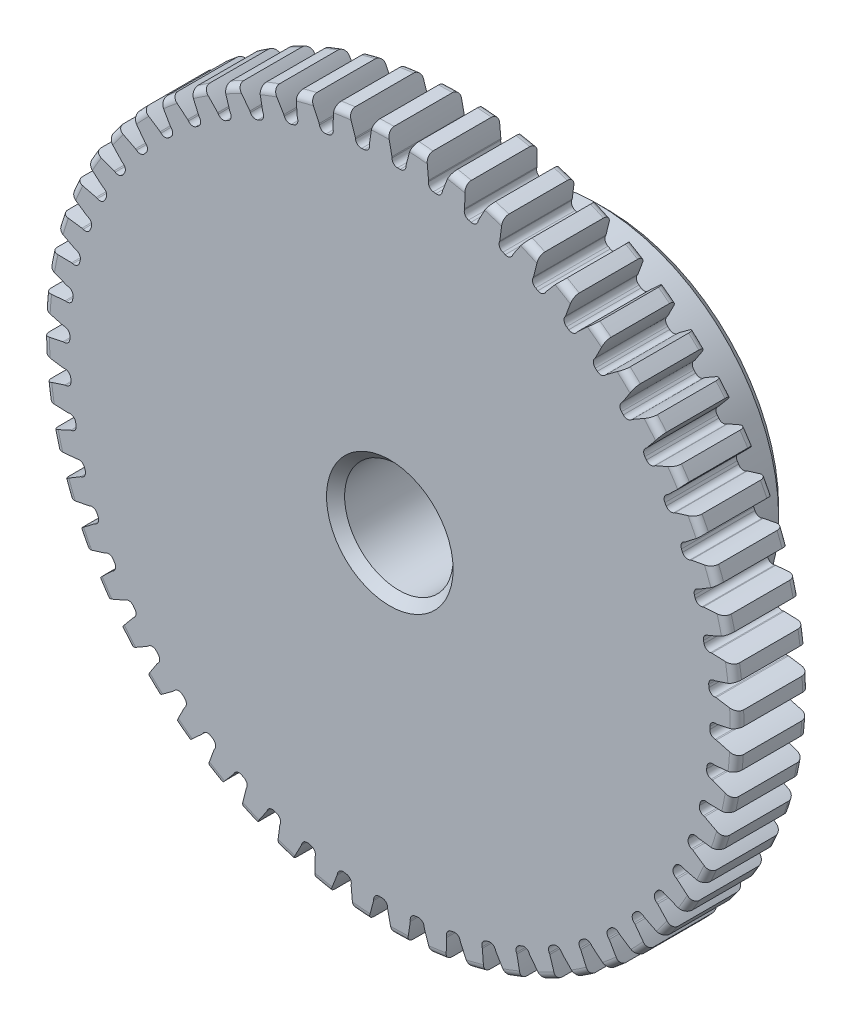
SolidWorks part; units mm, degrees
ref_plane "Front" through (0, 0, 0) normal (0, 0, 1) x (1, 0, 0)
ref_plane "Top" through (0, 0, 0) normal (0, 1, 0) x (1, 0, 0)
ref_plane "Right" through (0, 0, 0) normal (1, 0, 0) x (0, 0, -1)
sketch "Sketch1" plane through (0, 0, 0) normal (0, 0, 1) x (1, 0, 0)
  line L0 (-711.2, 0) -> (711.2, 0) construction
  circle A0 centre (0, 0) radius 15.24
  circle A1 centre (0, 0) radius 14.8209 construction
  circle A3 centre (0, 0) radius 14.049 construction
  dimension "D1" = 1.191
  dimension "OD" = 30.48
  dimension "Ptich Dia" = 29.6418
  dimension "Root Dia" = 28.0981
  dimension "D3" = 0.4191
  dimension "Number of Teeth" = 1422.4
extrude "Boss-Extrude1" add sketch "Sketch1" against normal blind 3.175
sketch "Sketch2" plane through (0, 0, 0) normal (1, 0, 0) x (0, 0, -1)
  line L0 (3.175, 0) -> (9.525, 0)
  line L1 (3.175, 0) -> (3.175, 7.9375)
  line L2 (3.175, 7.9375) -> (9.525, 7.9375)
  line L3 (9.525, 7.9375) -> (9.525, 0)
  point P5 (9.525, -7.9375)
  point P6 (0, -15.24)
  point P7 (3.175, -15.24)
  point P9 (0, 15.24)
  dimension "Face Wd" = 3.175
  dimension "B Hub Dia" = 15.875
  dimension "D O'all Lg." = 9.525
revolve "Revolve1" add sketch "Sketch2" angle 360 about L0
fillet "Fillet2" radius 0.3048 3 edges at (15.24, 0, -3.175) (15.24, 0, 0) (7.9375, 0, -3.175)
sketch "Sketch3" plane through (0, 0, 0) normal (0, 0, 1) x (1, 0, 0)
  line L0 (0, 0) -> (0, 15.24) construction
  line L1 (-3.5927, 13.8918) -> (0, 14.8209)
  line L2 (-9.5921, 14.8209) -> (9.5921, 14.8209) construction
  line L3 (-9.2865, 12.4192) -> (9.2865, 17.2226) construction
  line L4 (-3.5927, 13.8918) -> (0, 0) construction
  line L5 (-9.1637, 11.0416) -> (0, 0) construction
  line L6 (-9.1637, 11.0416) -> (-1.4732, 17.424) construction
  line L7 (-2.5051, 14.1284) -> (0, 0) construction
  line L8 (-2.5051, 14.1284) -> (0.0526, 14.582) construction
  arc A0 (-3.5927, 13.8918) -> (-9.1637, 11.0416) centre (0, 0) ccw
  circle A1 centre (0, 0) radius 14.8209 construction
  circle A2 centre (0, 0) radius 14.3488 construction
  arc A3 (-3.5927, 13.8918) -> (-2.5051, 14.1284) centre (0, 0) cw
  circle A4 centre (0, 0) radius 15.24 construction
  point P6 (0, 14.8209)
  dimension "D1" = 3.7109
  dimension "Pressure Angle" = 14.5
  dimension "D2" = 6.3085
  dimension "D3" = 9.9939
  dimension "D4" = 1.1133
  dimension "D5" = 2.5976
sketch "Sketch4" plane through (0, 0, 0) normal (0, 0, 1) x (1, 0, 0)
  line L0 (0, 0) -> (0.4155, 14.8092) construction
  line L1 (0.0932, 14.3485) -> (0.0932, 14.0487)
  line L2 (0, 14.8209) -> (0.831, 14.7976) construction
  line L3 (0.7115, 14.3312) -> (0.6947, 14.0319)
  line L4 (0.0932, 14.0487) -> (0, 0) construction
  line L5 (0, 0) -> (0, 15.24) construction
  line L6 (-9.1637, 11.0416) -> (-1.4732, 17.424) construction
  line L7 (-9.1637, 11.0416) -> (-1.4732, 17.424) construction
  arc A0 (0.6947, 14.0319) -> (0.0932, 14.0487) centre (0, 0) ccw
  arc A1 (0, 14.8209) -> (0.831, 14.7976) centre (0, 0) cw construction
  circle A2 centre (0, 0) radius 14.8209 construction
  circle A3 centre (0, 0) radius 14.3488 construction
  circle A4 centre (0, 0) radius 14.049 construction
  arc A5 (2.4479, 17.314) -> (-1.4732, 17.424) centre (0, 0) ccw
  spline S0 degree 2 poles (-1.4732, 17.424) (-0.168, 16.0666) (0.0932, 14.3485) knots 0 0 0 1 1 1
  spline S1 degree 2 poles (2.4479, 17.314) (1.0686, 16.0319) (0.7115, 14.3312) knots 0 0 0 1 1 1
  dimension "D1" = 0.8315
extrude "Cut-Extrude1" cut sketch "Sketch4" against normal through all
fillet "Fillet1" radius 0.2494 2 edges at (0.6947, 14.0319, -1.5875) (0.0932, 14.0487, -1.5875)
pattern_circular "CirPattern1" count 56 over 360 about axis through (0, 0, -3.175) along (0, 0, 1) of "Cut-Extrude1", "Fillet1"
sketch "Sketch5" plane through (0, 0, 0) normal (0, 0, 1) x (1, 0, 0)
  circle A0 centre (0, 0) radius 2.3813
  circle A1 centre (0, 0) radius 1.5875 construction
  dimension "Bore Min" = 4.7625
  dimension "Bore Max" = 3.175
extrude "Cut-Extrude2" cut sketch "Sketch5" against normal through all
chamfer "Chamfer1" distance 0.3969 angle 45 3 edges at (7.9375, 0, -9.525) (2.3813, 0, 0) (2.3813, 0, -9.525)
sketch "Pitch Dia" plane through (0, 0, 0) normal (0, 0, 1) x (1, 0, 0)
  circle A0 centre (0, 0) radius 14.8209 construction
  circle A1 centre (0, 0) radius 14.8209 construction
equation "\"D1@Boss-Extrude1\" = \"Face Wd@Sketch2\""
equation "\"D2@Sketch3\" = \"D1@Sketch3\"*1.7"
equation "\"D3@Sketch3\" = \"D1@Sketch3\"+\"D2@Sketch3\"-.001"
equation "\"D4@Sketch3\" = \"D1@Sketch3\"*.3"
equation "\"D5@Sketch3\" = \"D1@Sketch3\"-\"D4@Sketch3\""
equation "\"D1@Sketch4\" = 1.5708/(\"Number of Teeth@Sketch1\"/\"Ptich Dia@Sketch1\")"
equation "\"D1@Chamfer1\" = \"B Hub Dia@Sketch2\"*.025"
equation "\"D1@CirPattern1\" = \"Number of Teeth@Sketch1\""
equation "\"D1@Fillet1\" = \"D1@Sketch4\"*.3"
equation "\"D1@Fillet2\" = \"OD@Sketch1\"*.01"
equation "\"D1@Sketch1\" = 2.250/(\"Number of Teeth@Sketch1\"/\"Ptich Dia@Sketch1\")"
